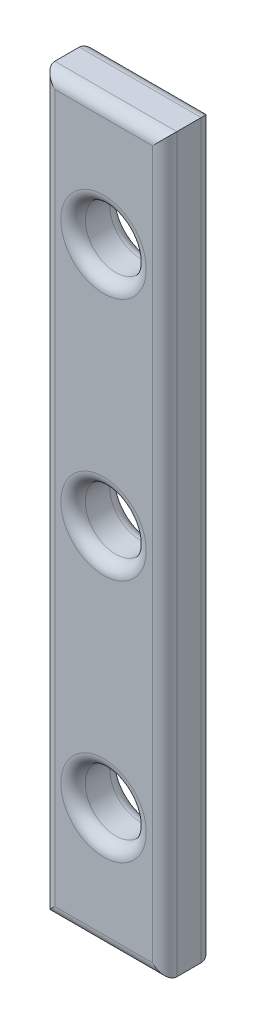
SolidWorks part; units mm, degrees
ref_plane "Front Plane" through (0, 0, 0) normal (0, 0, 1) x (1, 0, 0)
ref_plane "Top Plane" through (0, 0, 0) normal (0, 1, 0) x (1, 0, 0)
ref_plane "Right Plane" through (0, 0, 0) normal (1, 0, 0) x (0, 0, -1)
sketch "Sketch2" plane through (0, 0, 0) normal (0, 0, 1) x (1, 0, 0)
  line L1 (0, 0) -> (10, 0)
  line L2 (0, 0) -> (0, 60)
  line L3 (0, 60) -> (10, 60)
  line L4 (10, 0) -> (10, 60)
  circle A0 centre (5, 50) radius 2.5
  circle A1 centre (5, 10) radius 2.5
  circle A2 centre (5, 30) radius 2.5
extrude "Boss-Extrude1" add sketch "Sketch2" along normal blind 4
fillet "Fillet1" radius 1 13 edges at (7.5, 30, 4) (5, 60, 0) (7.5, 50, 0) (10, 30, 0) (7.5, 10, 0) (0, 30, 0) (5, 0, 0) (5, 0, 4) (7.5, 10, 4) (10, 30, 4) (7.5, 50, 4) (0, 30, 4) (5, 60, 4)
fillet "Fillet2" radius 1 1 edges at (7.5, 30, 0)
